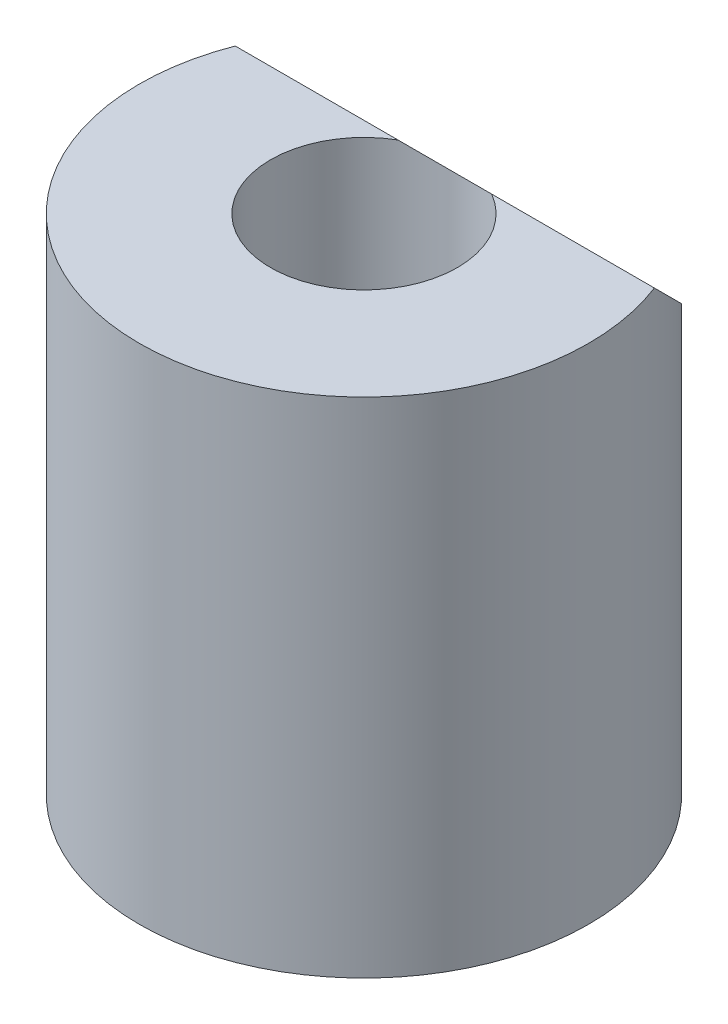
SolidWorks part; units mm, degrees
ref_plane "Front Plane" through (0, 0, 0) normal (0, 0, 1) x (1, 0, 0)
ref_plane "Top Plane" through (0, 0, 0) normal (0, 1, 0) x (1, 0, 0)
ref_plane "Right Plane" through (0, 0, 0) normal (1, 0, 0) x (0, 0, -1)
sketch "Sketch1" plane through (0, 0, 0) normal (0, 1, 0) x (1, 0, 0)
  circle A0 centre (0, 0) radius 6.25
  dimension "D1" = 12.5
extrude "Boss-Extrude1" add sketch "Sketch1" along normal blind 14
sketch "Sketch2" plane through (0, 14, 0) normal (0, 1, 0) x (1, 0, 0)
  circle A0 centre (0, 0) radius 2.6
  dimension "D1" = 5.2
extrude "Cut-Extrude1" cut sketch "Sketch2" against normal up to surface (14 mm away) up to face at (0, 0, 6.25)
ref_plane "Plane1" through (0, 0, 0) normal (1, 0, 0) x (0, 0, -1)
sketch "Sketch3" plane through (0, 0, 0) normal (1, 0, 0) x (0, 0, -1)
  line L0 (2.25, 14) -> (6.25, 10)
  line L1 (6.25, 0) -> (6.25, 14) construction
  line L2 (6.25, 14) -> (-6.25, 14) construction
  line L3 (6.25, 10) -> (6.25, 14)
  line L4 (6.25, 14) -> (2.25, 14)
  dimension "D1" = 45
  dimension "4" = 4
extrude "Cut-Extrude2" cut sketch "Sketch3" against normal mid plane 14
sketch "Sketch4" plane through (0, 0, 0) normal (0, -1, 0) x (1, 0, 0)
  circle A0 centre (0, 0) radius 4.5
  dimension "D1" = 9
extrude "Cut-Extrude3" cut sketch "Sketch4" against normal blind 4
